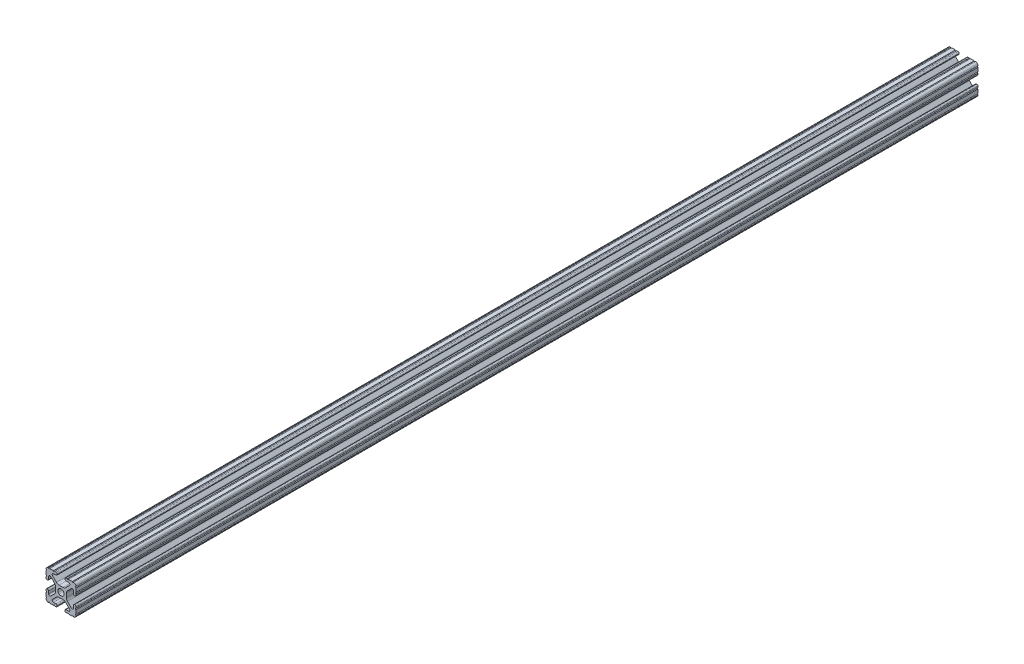
SolidWorks part; units mm, degrees
ref_plane "Front Plane" through (0, 0, 0) normal (0, 0, 1) x (1, 0, 0)
ref_plane "Top Plane" through (0, 0, 0) normal (0, 1, 0) x (1, 0, 0)
ref_plane "Right Plane" through (0, 0, 0) normal (1, 0, 0) x (0, 0, -1)
sketch "Sketch1" plane through (0, 0, 0) normal (0, 0, 1) x (1, 0, 0)
  line L88 (-7.1797, -8.6452) -> (-3.9523, -5.4237)
  line L89 (-1.7093, -4.4958) -> (1.7093, -4.4958)
  line L90 (3.9523, -5.4237) -> (7.1797, -8.6452)
  line L91 (6.4164, -10.4902) -> (4.2875, -10.4902)
  line L92 (3.2385, -11.5392) -> (3.2385, -11.651)
  line L93 (4.2875, -12.7) -> (5.3171, -12.7)
  line L94 (6.3331, -12.7) -> (9.5504, -12.7)
  line L95 (12.7, -9.5504) -> (12.7, -6.3331)
  line L96 (12.7, -5.3171) -> (12.7, -4.2875)
  line L97 (11.651, -3.2385) -> (11.5392, -3.2385)
  line L98 (10.4902, -4.2875) -> (10.4902, -6.4021)
  line L99 (8.7371, -7.1294) -> (5.441, -3.8408)
  line L100 (4.5085, -1.5932) -> (4.5085, 1.5932)
  line L101 (5.441, 3.8408) -> (8.7371, 7.1294)
  line L102 (10.4902, 6.4021) -> (10.4902, 4.2875)
  line L103 (11.5392, 3.2385) -> (11.651, 3.2385)
  line L104 (12.7, 4.2875) -> (12.7, 5.3171)
  line L105 (12.7, 6.3331) -> (12.7, 9.5504)
  line L106 (9.5504, 12.7) -> (6.3331, 12.7)
  line L107 (5.3171, 12.7) -> (4.2875, 12.7)
  line L108 (3.2385, 11.651) -> (3.2385, 11.5392)
  line L109 (4.2875, 10.4902) -> (6.4768, 10.4902)
  line L110 (7.207, 8.7244) -> (3.8983, 5.4232)
  line L111 (1.6558, 4.4958) -> (-1.6558, 4.4958)
  line L112 (-3.8983, 5.4232) -> (-7.207, 8.7244)
  line L113 (-6.4768, 10.4902) -> (-4.2875, 10.4902)
  line L114 (-3.2385, 11.5392) -> (-3.2385, 11.651)
  line L115 (-4.2875, 12.7) -> (-5.3171, 12.7)
  line L116 (-6.3331, 12.7) -> (-9.5504, 12.7)
  line L117 (-12.7, 9.5504) -> (-12.7, 6.3331)
  line L118 (-12.7, 5.3171) -> (-12.7, 4.2875)
  line L119 (-11.651, 3.2385) -> (-11.5392, 3.2385)
  line L120 (-10.4902, 4.2875) -> (-10.4902, 6.4021)
  line L121 (-8.7371, 7.1294) -> (-5.441, 3.8408)
  line L122 (-4.5085, 1.5932) -> (-4.5085, -1.5932)
  line L123 (-5.441, -3.8408) -> (-8.7371, -7.1294)
  line L124 (-10.4902, -6.4021) -> (-10.4902, -4.2875)
  line L125 (-11.5392, -3.2385) -> (-11.651, -3.2385)
  line L126 (-12.7, -4.2875) -> (-12.7, -5.3171)
  line L127 (-12.7, -6.3331) -> (-12.7, -9.5504)
  line L128 (-9.5504, -12.7) -> (-6.3331, -12.7)
  line L129 (-5.3171, -12.7) -> (-4.2875, -12.7)
  line L130 (-3.2385, -11.651) -> (-3.2385, -11.5392)
  line L131 (-4.2875, -10.4902) -> (-6.4164, -10.4902)
  circle A1 centre (0, 0) radius 2.6035
  arc A104 (-7.1797, -8.6452) -> (-6.4164, -10.4902) centre (-6.4164, -9.4098) ccw
  arc A105 (-1.7093, -4.4958) -> (-3.9523, -5.4237) centre (-1.7093, -7.6708) ccw
  arc A106 (3.9523, -5.4237) -> (1.7093, -4.4958) centre (1.7093, -7.6708) ccw
  arc A107 (6.4164, -10.4902) -> (7.1797, -8.6452) centre (6.4164, -9.4098) ccw
  arc A108 (4.2875, -10.4902) -> (3.2385, -11.5392) centre (4.2875, -11.5392) ccw
  arc A109 (3.2385, -11.651) -> (4.2875, -12.7) centre (4.2875, -11.651) ccw
  arc A110 (6.3331, -12.7) -> (5.3171, -12.7) centre (5.8251, -12.7) ccw
  arc A111 (10.5664, -12.6998) -> (9.5504, -12.7) centre (10.0584, -12.7) ccw
  arc A112 (10.5664, -12.6998) -> (12.6998, -10.5664) centre (10.5918, -10.5918) ccw
  arc A113 (12.7, -9.5504) -> (12.6998, -10.5664) centre (12.7, -10.0584) ccw
  arc A114 (12.7, -5.3171) -> (12.7, -6.3331) centre (12.7, -5.8251) ccw
  arc A115 (12.7, -4.2875) -> (11.651, -3.2385) centre (11.651, -4.2875) ccw
  arc A116 (11.5392, -3.2385) -> (10.4902, -4.2875) centre (11.5392, -4.2875) ccw
  arc A117 (8.7371, -7.1294) -> (10.4902, -6.4021) centre (9.4628, -6.4021) ccw
  arc A118 (4.5085, -1.5932) -> (5.441, -3.8408) centre (7.6835, -1.5932) ccw
  arc A119 (5.441, 3.8408) -> (4.5085, 1.5932) centre (7.6835, 1.5932) ccw
  arc A120 (10.4902, 6.4021) -> (8.7371, 7.1294) centre (9.4628, 6.4021) ccw
  arc A121 (10.4902, 4.2875) -> (11.5392, 3.2385) centre (11.5392, 4.2875) ccw
  arc A122 (11.651, 3.2385) -> (12.7, 4.2875) centre (11.651, 4.2875) ccw
  arc A123 (12.7, 6.3331) -> (12.7, 5.3171) centre (12.7, 5.8251) ccw
  arc A124 (12.6998, 10.5664) -> (12.7, 9.5504) centre (12.7, 10.0584) ccw
  arc A125 (12.6998, 10.5664) -> (10.5664, 12.6998) centre (10.5918, 10.5918) ccw
  arc A126 (9.5504, 12.7) -> (10.5664, 12.6998) centre (10.0584, 12.7) ccw
  arc A127 (5.3171, 12.7) -> (6.3331, 12.7) centre (5.8251, 12.7) ccw
  arc A128 (4.2875, 12.7) -> (3.2385, 11.651) centre (4.2875, 11.651) ccw
  arc A129 (3.2385, 11.5392) -> (4.2875, 10.4902) centre (4.2875, 11.5392) ccw
  arc A130 (7.207, 8.7244) -> (6.4768, 10.4902) centre (6.4768, 9.4563) ccw
  arc A131 (1.6558, 4.4958) -> (3.8983, 5.4232) centre (1.6558, 7.6708) ccw
  arc A132 (-3.8983, 5.4232) -> (-1.6558, 4.4958) centre (-1.6558, 7.6708) ccw
  arc A133 (-6.4768, 10.4902) -> (-7.207, 8.7244) centre (-6.4768, 9.4563) ccw
  arc A134 (-4.2875, 10.4902) -> (-3.2385, 11.5392) centre (-4.2875, 11.5392) ccw
  arc A135 (-3.2385, 11.651) -> (-4.2875, 12.7) centre (-4.2875, 11.651) ccw
  arc A136 (-6.3331, 12.7) -> (-5.3171, 12.7) centre (-5.8251, 12.7) ccw
  arc A137 (-10.5664, 12.6998) -> (-9.5504, 12.7) centre (-10.0584, 12.7) ccw
  arc A138 (-10.5664, 12.6998) -> (-12.6998, 10.5664) centre (-10.5918, 10.5918) ccw
  arc A139 (-12.7, 9.5504) -> (-12.6998, 10.5664) centre (-12.7, 10.0584) ccw
  arc A140 (-12.7, 5.3171) -> (-12.7, 6.3331) centre (-12.7, 5.8251) ccw
  arc A141 (-12.7, 4.2875) -> (-11.651, 3.2385) centre (-11.651, 4.2875) ccw
  arc A142 (-11.5392, 3.2385) -> (-10.4902, 4.2875) centre (-11.5392, 4.2875) ccw
  arc A143 (-8.7371, 7.1294) -> (-10.4902, 6.4021) centre (-9.4628, 6.4021) ccw
  arc A144 (-4.5085, 1.5932) -> (-5.441, 3.8408) centre (-7.6835, 1.5932) ccw
  arc A145 (-5.441, -3.8408) -> (-4.5085, -1.5932) centre (-7.6835, -1.5932) ccw
  arc A146 (-10.4902, -6.4021) -> (-8.7371, -7.1294) centre (-9.4628, -6.4021) ccw
  arc A147 (-10.4902, -4.2875) -> (-11.5392, -3.2385) centre (-11.5392, -4.2875) ccw
  arc A148 (-11.651, -3.2385) -> (-12.7, -4.2875) centre (-11.651, -4.2875) ccw
  arc A149 (-12.7, -6.3331) -> (-12.7, -5.3171) centre (-12.7, -5.8251) ccw
  arc A150 (-12.6998, -10.5664) -> (-12.7, -9.5504) centre (-12.7, -10.0584) ccw
  arc A151 (-12.6998, -10.5664) -> (-10.5664, -12.6998) centre (-10.5918, -10.5918) ccw
  arc A152 (-9.5504, -12.7) -> (-10.5664, -12.6998) centre (-10.0584, -12.7) ccw
  arc A153 (-5.3171, -12.7) -> (-6.3331, -12.7) centre (-5.8251, -12.7) ccw
  arc A154 (-4.2875, -12.7) -> (-3.2385, -11.651) centre (-4.2875, -11.651) ccw
  arc A155 (-3.2385, -11.5392) -> (-4.2875, -10.4902) centre (-4.2875, -11.5392) ccw
extrude "Boss-Extrude1" add sketch "Sketch1" along normal mid plane 762
